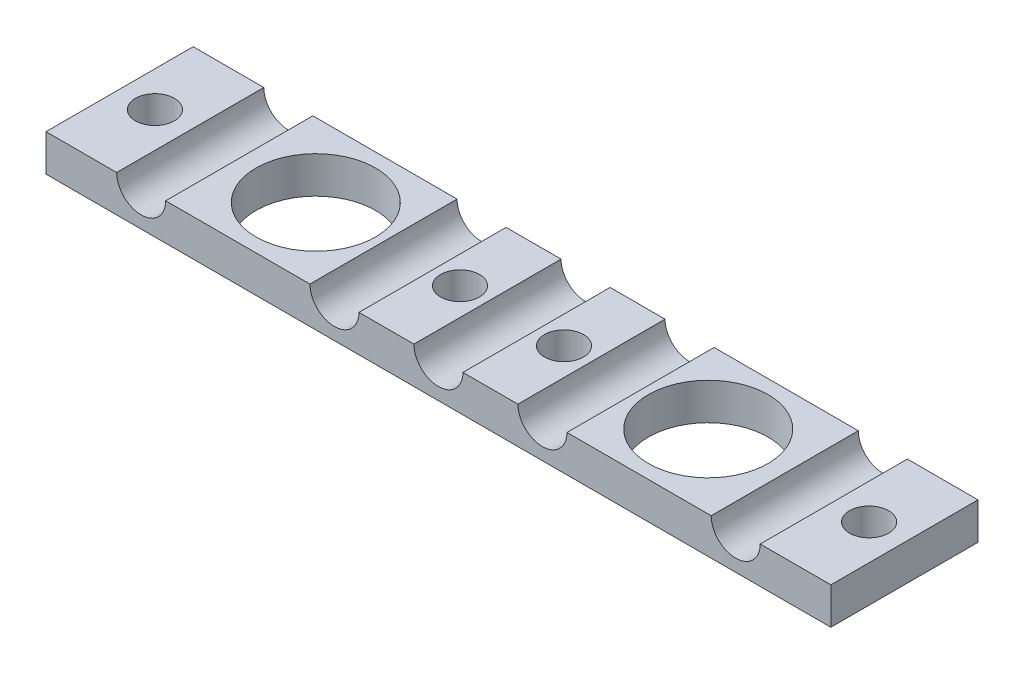
SolidWorks part; units mm, degrees
material "FLUOROELASTOMER"
ref_plane "Front Plane" through (0, 0, 0) normal (0, 0, 1) x (1, 0, 0)
ref_plane "Top Plane" through (0, 0, 0) normal (0, 1, 0) x (1, 0, 0)
ref_plane "Right Plane" through (0, 0, 0) normal (1, 0, 0) x (0, 0, -1)
sketch "Sketch1" plane through (0, 0, 0) normal (0, 1, 0) x (1, 0, 0)
  line L0 (0, 0) -> (-50.8, 0) construction
  line L1 (-50.8, 9.525) -> (50.8, 9.525)
  line L2 (-50.8, 9.525) -> (-50.8, -9.525)
  line L3 (-50.8, -9.525) -> (50.8, -9.525)
  line L4 (50.8, 9.525) -> (50.8, -9.525)
  line L5 (0, 0) -> (0, 9.525) construction
  dimension "D1" = 101.6
  dimension "D2" = 19.05
extrude "Extrude1" add sketch "Sketch1" along normal blind 4.7625
hole_wizard "39/64 (0.60938) Diameter Hole1" positions "Sketch3" profile "Sketch2" hole size "39/64" standard "Ansi Inch" end condition through all
sketch "Sketch3" plane through (0, 4.7625, 0) normal (0, 1, 0) x (-1, 0, 0)
  line L0 (25.4, 0) -> (-25.4, 0) construction
  line L1 (2.6194, 0) -> (-2.6194, 0) construction
  point P0 (25.4, 0)
  point P1 (-25.4, 0)
  dimension "D1" = 25.4
  dimension "D2" = 50.8
sketch "Sketch2" plane through (-25.4, 4.7625, 0) normal (1, 0, 0) x (0, 0, 1)
  line L0 (0, 0) -> (0, 4.7625)
  line L1 (0, 4.7625) -> (7.7391, 4.7625)
  line L2 (7.7391, 4.7625) -> (7.7391, 0)
  line L5 (7.7391, 0) -> (0, 0)
  line L11 (0, -6.35) -> (0, 107.95) construction
  dimension "Thru Hole Dia." = 15.4783
  dimension "Thru Hole Depth" = 4.7625
hole_wizard "1/4 (0.25) Diameter Hole1" positions "Sketch5" profile "Sketch4" hole size "1/4" standard "Ansi Inch" end condition through all
sketch "Sketch5" plane through (0, 0, 9.525) normal (0, 0, 1) x (1, 0, 0)
  line L0 (-38.481, 4.7625) -> (-13.462, 4.7625) construction
  line L1 (-13.462, 4.7625) -> (0, 4.7625) construction
  line L2 (0, 4.7625) -> (13.462, 4.7625) construction
  line L3 (13.462, 4.7625) -> (38.481, 4.7625) construction
  line L4 (-50.8, 4.7625) -> (50.8, 4.7625) construction
  line L5 (0, 0) -> (0, 4.7625) construction
  point P0 (0, 4.7625)
  point P1 (-13.462, 4.7625)
  point P3 (13.462, 4.7625)
  point P5 (-38.481, 4.7625)
  point P7 (38.481, 4.7625)
  dimension "D1" = 38.481
  dimension "D2" = 13.462
sketch "Sketch4" plane through (0, 4.7625, 9.525) normal (1, 0, 0) x (0, -1, 0)
  line L0 (0, 0) -> (0, 19.05)
  line L1 (0, 19.05) -> (3.175, 19.05)
  line L2 (3.175, 19.05) -> (3.175, 0)
  line L5 (3.175, 0) -> (0, 0)
  line L11 (0, -6.35) -> (0, 107.95) construction
  dimension "Thru Hole Dia." = 6.35
  dimension "Thru Hole Depth" = 19.05
hole_wizard "#8 (0.199) Diameter Hole1" positions "Sketch7" profile "Sketch6" hole size "#8" standard "Ansi Inch" end condition through all
sketch "Sketch7" plane through (0, 4.7625, 0) normal (0, 1, 0) x (-1, 0, 0)
  line L0 (-50.8, 0) -> (-46.228, 0) construction
  line L1 (-50.8, 9.525) -> (-50.8, -9.525) construction
  line L2 (-46.228, 0) -> (-6.731, 0) construction
  line L3 (-6.731, 0) -> (6.731, 0) construction
  line L4 (6.731, 0) -> (46.228, 0) construction
  line L5 (46.228, -9.525) -> (46.228, 0) construction
  line L6 (41.656, -9.525) -> (50.8, -9.525) construction
  line L7 (6.731, -9.525) -> (6.731, 0) construction
  line L8 (3.175, -9.525) -> (10.287, -9.525) construction
  line L9 (-6.731, -9.525) -> (-6.731, 0) construction
  line L10 (-10.287, -9.525) -> (-3.175, -9.525) construction
  line L11 (-46.228, -9.525) -> (-46.228, 0) construction
  line L12 (-50.8, -9.525) -> (-41.656, -9.525) construction
  point P0 (-46.228, 0)
  point P1 (-6.731, 0)
  point P3 (6.731, 0)
  point P5 (46.228, 0)
sketch "Sketch6" plane through (46.228, 4.7625, 0) normal (1, 0, 0) x (0, 0, 1)
  line L0 (0, 0) -> (0, 4.7625)
  line L1 (0, 4.7625) -> (2.5273, 4.7625)
  line L2 (2.5273, 4.7625) -> (2.5273, 0)
  line L5 (2.5273, 0) -> (0, 0)
  line L11 (0, -6.35) -> (0, 107.95) construction
  dimension "Thru Hole Dia." = 5.0546
  dimension "Thru Hole Depth" = 4.7625
